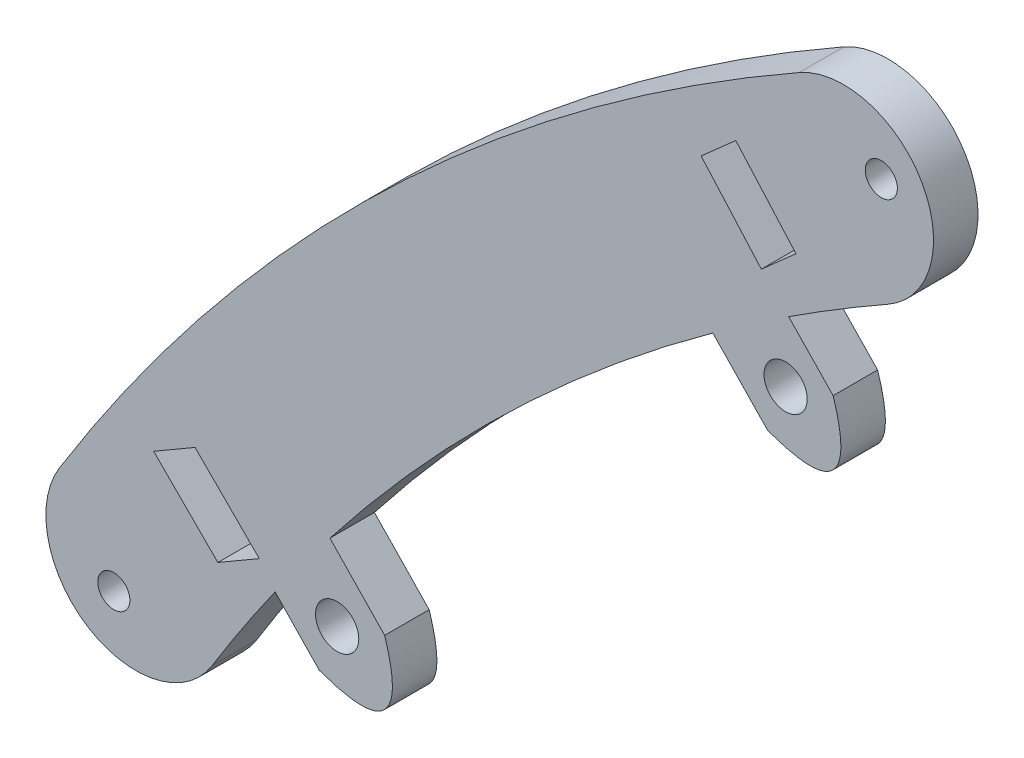
SolidWorks part; units mm, degrees
ref_plane "Front Plane" through (0, 0, 0) normal (0, 0, 1) x (1, 0, 0)
ref_plane "Top Plane" through (0, 0, 0) normal (0, 1, 0) x (1, 0, 0)
ref_plane "Right Plane" through (0, 0, 0) normal (1, 0, 0) x (0, 0, -1)
sketch "Sketch1" plane through (0, 0, 0) normal (0, 0, 1) x (1, 0, 0)
  line L0 (79.3567, 59.8752) -> (74.4144, 55.495) construction
  line L1 (-2.1009, -11.7887) -> (7.0606, -20.9502)
  line L2 (-2.1009, -11.7887) -> (-8.0109, -15.2182)
  line L3 (13.1734, -18.5938) -> (24.8681, -30.7387) construction
  line L4 (77.1692, 43.0921) -> (88.0824, 30.3327) construction
  line L5 (-8.0109, -15.2182) -> (1.1506, -24.3797)
  line L6 (15.6218, -30.4742) -> (9.3177, -23.9275)
  line L7 (24.9529, -21.4889) -> (17.1417, -13.377)
  line L8 (7.0606, -20.9502) -> (1.1506, -24.3797)
  line L9 (19.5569, -31.5903) -> (16.4789, -14.2302) construction
  line L10 (25.7607, -25.429) -> (10.5857, -22.143) construction
  line L11 (15.6218, -30.4742) -> (24.9529, -21.4889) construction
  line L12 (75.0608, 64.7225) -> (83.6527, 55.0279)
  line L13 (79.6257, 31.1572) -> (71.7848, 39.2999)
  line L14 (88.9569, 40.1425) -> (82.6127, 46.7309)
  line L15 (75.0608, 64.7225) -> (70.1184, 60.3423)
  line L16 (83.5609, 30.0412) -> (80.8114, 45.5479) construction
  line L17 (91.7195, 35.7791) -> (72.6348, 39.9117) construction
  line L18 (79.6257, 31.1572) -> (88.9569, 40.1425) construction
  line L19 (70.1184, 60.3423) -> (78.7104, 50.6477)
  line L20 (83.6527, 55.0279) -> (78.7104, 50.6477)
  line L21 (2.4798, -16.3694) -> (-3.4301, -19.7989) construction
  arc A0 (-10.5653, -30.7733) -> (90.4609, 66.5081) centre (229.6747, -179.1632) cw construction
  arc A1 (84.1371, 77.6678) -> (-21.4784, -24.0326) centre (229.6747, -179.1632) ccw
  arc A2 (96.7848, 55.3483) -> (0.3477, -37.514) centre (229.6747, -179.1632) ccw
  arc A3 (96.7848, 55.3483) -> (84.1371, 77.6678) centre (90.4609, 66.5081) ccw
  arc A4 (-21.4784, -24.0326) -> (0.3477, -37.514) centre (-10.5653, -30.7733) ccw
  circle A5 centre (18.1732, -23.786) radius 3.0861
  circle A6 centre (82.1771, 37.8454) radius 3.0861
  circle A7 centre (-13.6994, -35.344) radius 2.2924
  circle A8 centre (95.8325, 70.3376) radius 2.2923
  spline S0 degree 2 poles (15.6218, -30.4742) (29.4488, -35.4957) (24.9529, -21.4889) knots 0 0 0 1 1 1
  spline S1 degree 2 poles (79.6257, 31.1572) (93.4528, 26.1357) (88.9569, 40.1425) knots 0 0 0 1 1 1
  point P0 (-17.306, -41.6864)
  point P1 (101.6207, 72.8319)
  point P11 (33.812, 24.2394)
  point P19 (18.1732, -23.786)
  point P31 (82.1771, 37.8454)
  point P56 (0.9437, -14.8333)
  dimension "D1" = 25.654
  dimension "D5" = 6.1722
  dimension "D9" = 6.1722
  dimension "D4" = 4.5847
  dimension "D6" = 4.5847
  dimension "D2" = 165.1
  dimension "D3" = 12.954
  dimension "D7" = 12.954
  dimension "D8" = 6.604
  dimension "D10" = 12.5222
  dimension "D11" = 6.604
  dimension "D12" = 12.954
extrude "Boss-Extrude1" add sketch "Sketch1" along normal blind 6.35 contours A1 A4 A2 A3 A8 A7 | L6 S0 L7 A2 A5 | L13 S1 L14 A2 A6
equation "\"kerf\"= .01"
